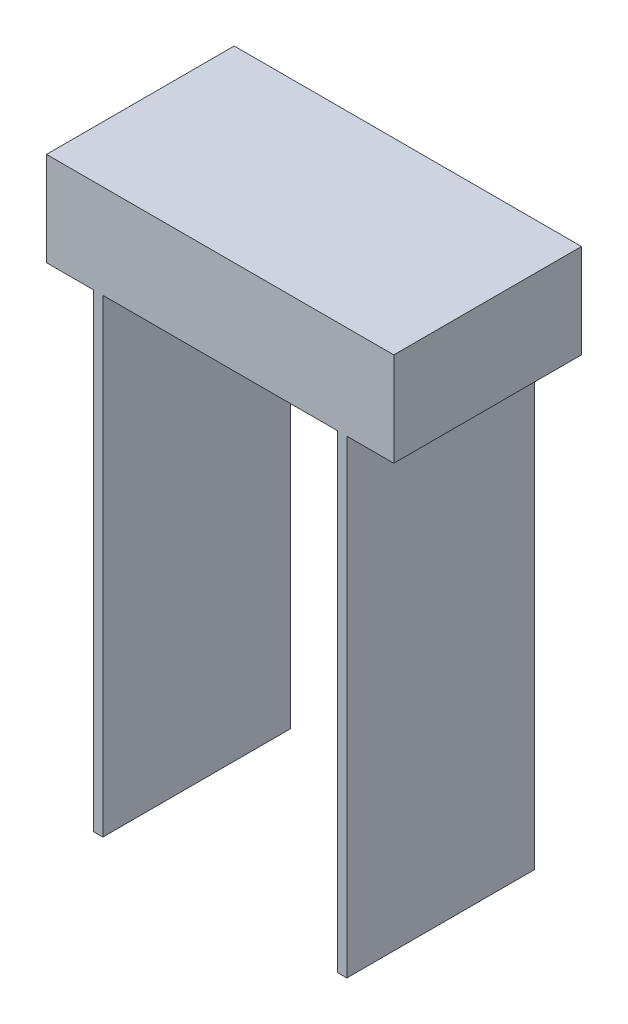
SolidWorks part; units mm, degrees
ref_plane "Front Plane" through (0, 0, 0) normal (0, 0, 1) x (1, 0, 0)
ref_plane "Top Plane" through (0, 0, 0) normal (0, 1, 0) x (1, 0, 0)
ref_plane "Right Plane" through (0, 0, 0) normal (1, 0, 0) x (0, 0, -1)
sketch "Sketch1" plane through (0, 0, 0) normal (0, 0, 1) x (1, 0, 0)
  line L0 (-10.6234, -7.8701) -> (-10.2234, -7.8701)
  line L1 (-10.2234, -7.8701) -> (-10.2234, 12.1299)
  line L2 (-10.2234, 12.1299) -> (-0.2234, 12.1299)
  line L3 (-0.2234, 12.1299) -> (-0.2234, -7.8701)
  line L4 (-0.2234, -7.8701) -> (0.1766, -7.8701)
  line L5 (0.1766, -7.8701) -> (0.1766, 12.1299)
  line L6 (0.1766, 12.1299) -> (2.1766, 12.1299)
  line L7 (2.1766, 12.1299) -> (2.1766, 16.1299)
  line L8 (2.1766, 16.1299) -> (-12.6234, 16.1299)
  line L9 (-12.6234, 16.1299) -> (-12.6234, 12.1299)
  line L10 (-12.6234, 12.1299) -> (-10.6234, 12.1299)
  line L11 (-10.6234, 12.1299) -> (-10.6234, -7.8701)
  dimension "D1" = 20
  dimension "D2" = 0.4
  dimension "D3" = 0.4
  dimension "D4" = 10
  dimension "D5" = 2
  dimension "D6" = 2
  dimension "D7" = 4
extrude "Boss-Extrude1" add sketch "Sketch1" along normal blind 8
